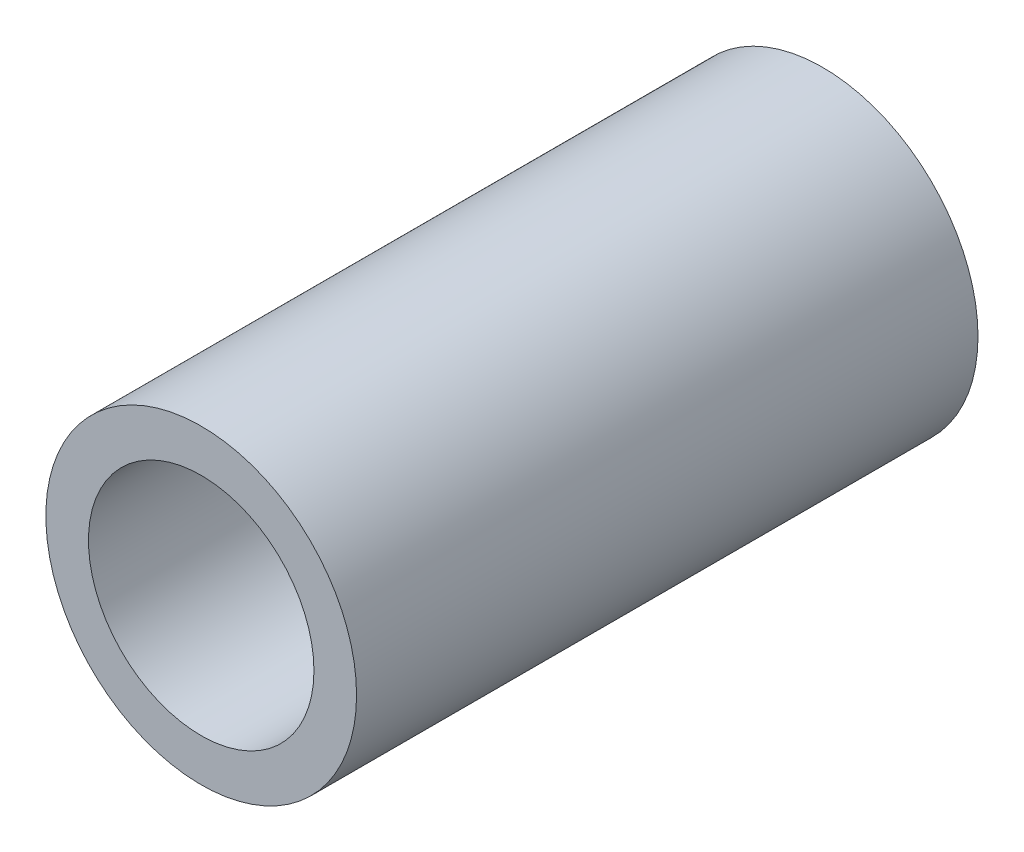
SolidWorks part; units mm, degrees
material "Delrin (Acetal)"
ref_plane "Front Plane" through (0, 0, 0) normal (0, 0, 1) x (1, 0, 0)
ref_plane "Top Plane" through (0, 0, 0) normal (0, 1, 0) x (1, 0, 0)
ref_plane "Right Plane" through (0, 0, 0) normal (1, 0, 0) x (0, 0, -1)
sketch "Sketch1" plane through (0, 0, 0) normal (0, 0, 1) x (1, 0, 0)
  circle A0 centre (0, 0) radius 11.1125
  circle A1 centre (0, 0) radius 8.0645
  dimension "D1" = 16.129
  dimension "Diameter" = 22.225
extrude "Extrude1" add sketch "Sketch1" along normal mid plane 44.45
